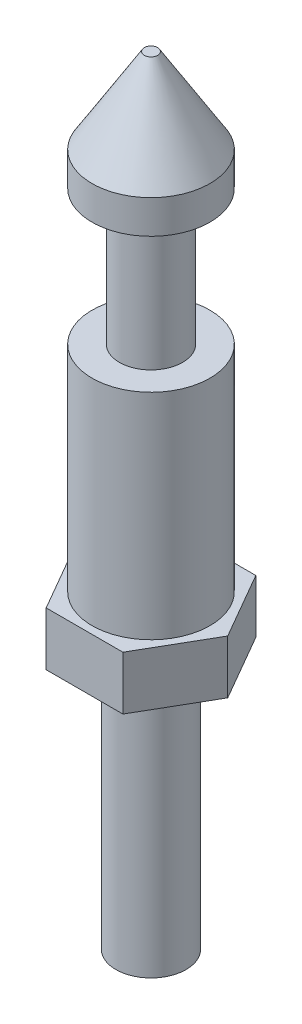
SolidWorks part; units mm, degrees
ref_plane "Front Plane" through (0, 0, 0) normal (0, 0, 1) x (1, 0, 0)
ref_plane "Top Plane" through (0, 0, 0) normal (0, 1, 0) x (1, 0, 0)
ref_plane "Right Plane" through (0, 0, 0) normal (1, 0, 0) x (0, 0, -1)
sketch "Sketch1" plane through (0, 0, 0) normal (0, 0, 1) x (1, 0, 0)
  line L0 (0, 0) -> (0, 79.052) construction
  line L1 (0, 0) -> (1.6637, 0)
  line L2 (1.6637, 0) -> (1.6637, 12.1412)
  line L3 (1.6637, 12.1412) -> (2.794, 12.1412)
  line L4 (2.794, 12.1412) -> (2.794, 24.8412)
  line L5 (2.794, 24.8412) -> (1.4986, 24.8412)
  line L6 (1.4986, 24.8412) -> (1.4986, 31.242)
  line L7 (1.4986, 31.242) -> (2.794, 31.242)
  line L8 (2.794, 31.242) -> (2.794, 32.8295)
  line L9 (2.794, 32.8295) -> (0.3175, 36.8554)
  line L10 (0.3175, 36.8554) -> (0, 36.8554)
  line L11 (0, 36.8554) -> (0, 0)
  dimension "D1" = 12.1412
  dimension "D2" = 12.7
  dimension "D3" = 6.4008
  dimension "D4" = 1.5875
  dimension "D5" = 24.7142
  dimension "D6" = 5.588
  dimension "D7" = 0.635
  dimension "D8" = 2.9972
  dimension "D9" = 5.588
  dimension "D10" = 3.3274
revolve "Revolve1" add sketch "Sketch1" angle 360 about L0
sketch "Sketch2" plane through (0, 12.1412, 0) normal (0, -1, 0) x (1, 0, 0)
  line L0 (0, 0) -> (3.6368, 0) construction
  line L1 (3.6368, 0) -> (1.8184, 3.1496)
  line L2 (1.8184, 3.1496) -> (-1.8184, 3.1496)
  line L3 (-1.8184, 3.1496) -> (-3.6368, 0)
  line L4 (-3.6368, 0) -> (-1.8184, -3.1496)
  line L5 (-1.8184, -3.1496) -> (1.8184, -3.1496)
  line L6 (1.8184, -3.1496) -> (3.6368, 0)
  circle A0 centre (0, 0) radius 3.1496 construction
  dimension "D1" = 6.2992
extrude "Boss-Extrude1" add sketch "Sketch2" against normal blind 2.54
sketch "Sketch3" plane through (0, 0, 0) normal (0, 0, 1) x (1, 0, 0)
  line L0 (1.4986, 24.8412) -> (1.4986, 31.242) construction
  line L1 (1.4986, 24.8412) -> (1.4986, 31.242)
  line L2 (1.4986, 31.242) -> (3.0226, 31.242)
  line L3 (1.4986, 24.8412) -> (3.0226, 24.8412)
  arc A0 (3.0226, 31.242) -> (3.0226, 24.8412) centre (3.0226, 28.0416) cw
  dimension "D1" = 1.524
revolve "Revolve2-Mini_Post_Rubber_supress" [suppressed] add sketch "Sketch3" angle 360
ref_plane "Plane1" through (0, 28.0162, 0) normal (0, 1, 0) x (1, 0, 0)
sketch "Sketch4" plane through (0, 28.0162, 0) normal (0, 1, 0) x (1, 0, 0)
  circle A0 centre (0, 0) radius 4.0386 construction
  dimension "D1" = 8.0772
